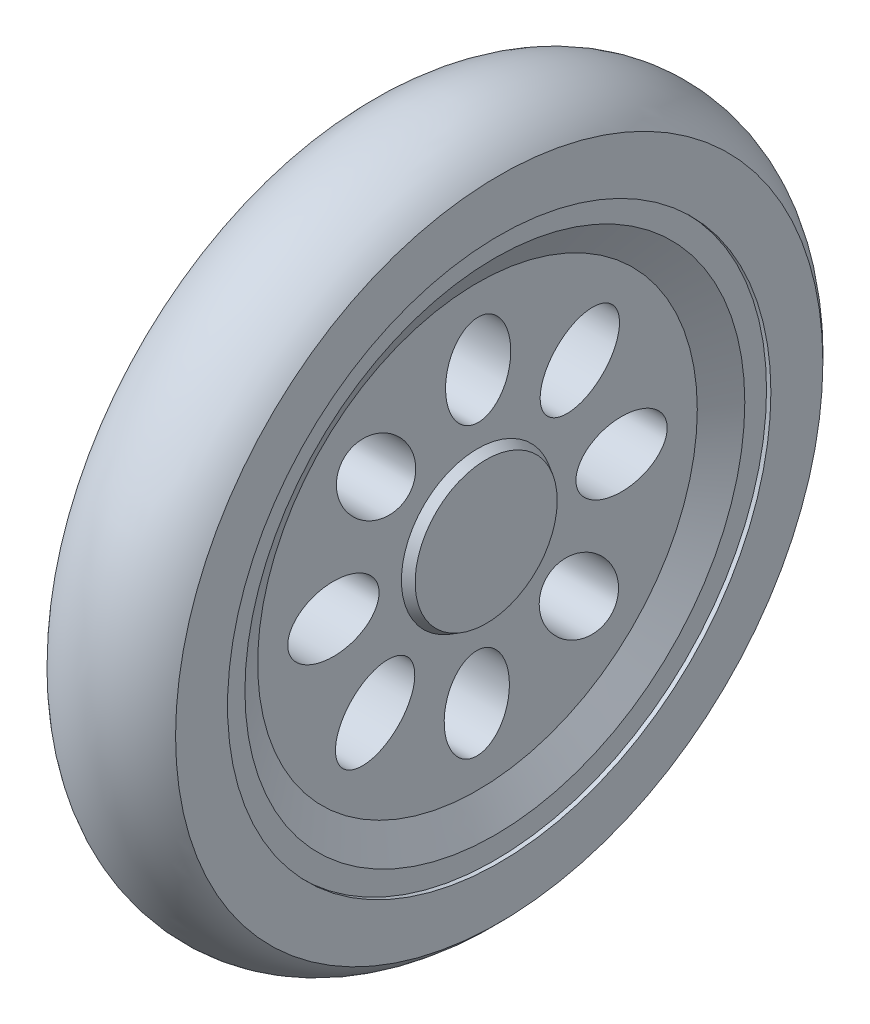
SolidWorks part; units mm, degrees
ref_plane "Front Plane" through (0, 0, 0) normal (0, 0, 1) x (1, 0, 0)
ref_plane "Top Plane" through (0, 0, 0) normal (0, 1, 0) x (1, 0, 0)
ref_plane "Right Plane" through (0, 0, 0) normal (1, 0, 0) x (0, 0, -1)
sketch "Sketch1" plane through (0, 0, 0) normal (1, 0, 0) x (0, 0, -1)
  circle A0 centre (0, 0) radius 41.25
  dimension "D1" = 82.5
extrude "Boss-Extrude1" add sketch "Sketch1" along normal blind 15
sketch "Sketch2" plane through (15, 0, 0) normal (1, 0, 0) x (0, 0, -1)
  circle A0 centre (0, 0) radius 31.75
  dimension "D1" = 63.5
extrude "Cut-Extrude1" cut sketch "Sketch2" against normal blind 0.508
sketch "Sketch3" plane through (14.492, 0, 0) normal (1, 0, 0) x (0, 0, -1)
  circle A0 centre (0, 0) radius 29.21
  circle A1 centre (0, 0) radius 31.75 construction
  dimension "D1" = 2.54
extrude "Cut-Extrude2" cut sketch "Sketch3" against normal blind 2.032 draft 60
sketch "Sketch4" plane through (12.46, 0, 0) normal (1, 0, 0) x (0, 0, -1)
  circle A0 centre (0, 0) radius 8.89
  dimension "D1" = 17.78
extrude "Boss-Extrude3" add sketch "Sketch4" along normal blind 1.016 draft 30
sketch "Sketch5" plane through (12.46, 0, 0) normal (1, 0, 0) x (0, 0, -1)
  ellipse E0 centre (0.0796, 16.8369) end of major axis (0.0796, 11.5029) minor radius 3.81
extrude "Cut-Extrude3" cut sketch "Sketch5" against normal through all
pattern_circular "CirPattern1" count 8 over 360 about axis through (13.476, 0, 0) along (1, 0, 0) of "Cut-Extrude3"
sketch "Sketch6" plane through (0, 0, 0) normal (-1, 0, 0) x (0, 0, 1)
  circle A0 centre (0, 0) radius 35.408
  circle A1 centre (0, 0) radius 41.25 construction
  dimension "D1" = 5.842
extrude "Cut-Extrude4" cut sketch "Sketch6" against normal blind 2.286
sketch "Sketch7" plane through (0, 0, 0) normal (0, 0, 1) x (1, 0, 0)
  line L0 (7.5, 41.25) -> (0, 41.25)
  line L1 (15, 41.25) -> (0, 41.25) construction
  line L2 (0, 41.25) -> (0, 37.8238)
  line L3 (15, 41.25) -> (15, 37.8238)
  line L4 (7.5, 41.25) -> (15, 41.25)
  arc A0 (15, 37.8238) -> (0, 37.8238) centre (7.5, 31.3003) ccw
ref_axis "Axis1" through (0, 0, 0) along (1, 0, 0)
revolve "Cut-Revolve1" cut sketch "Sketch7" angle 360 about axis through (0, 0, 0) along (1, 0, 0)
